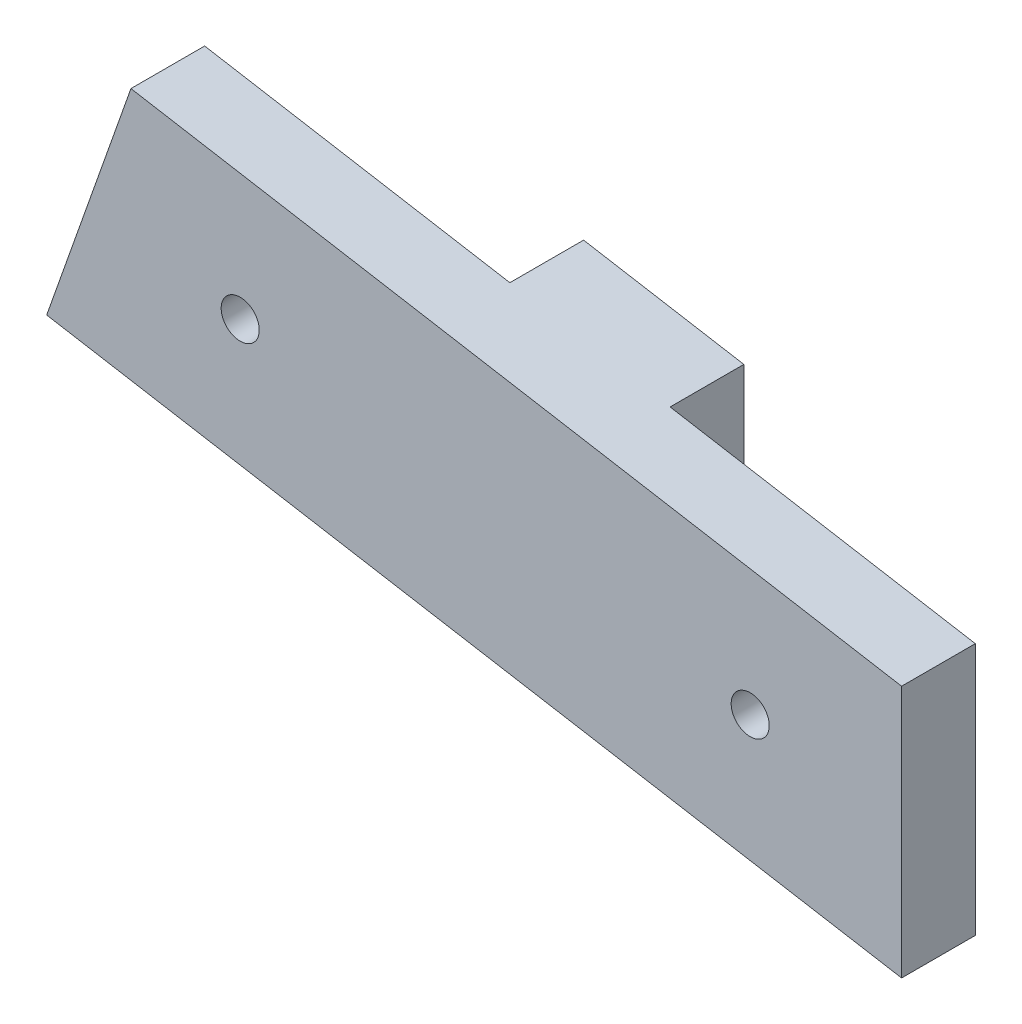
SolidWorks part; units mm, degrees
ref_plane "Спереди" through (0, 0, 0) normal (0, 0, 1) x (1, 0, 0)
ref_plane "Сверху" through (0, 0, 0) normal (0, 1, 0) x (1, 0, 0)
ref_plane "Справа" through (0, 0, 0) normal (1, 0, 0) x (0, 0, -1)
sketch "Эскиз1" plane through (0, 0, 0) normal (0, 0, 1) x (1, 0, 0)
  line L0 (-114.3235, 125.814) -> (-183.8951, 137.7528)
  line L1 (-183.8951, 137.7528) -> (-177.0391, 157.1408)
  line L2 (-177.0391, 157.1408) -> (-114.3235, 146.3785)
  line L3 (-114.3235, 146.3785) -> (-114.3235, 125.814)
extrude "Бобышка-Вытянуть1" add sketch "Эскиз1" along normal blind 6
sketch "Эскиз2" plane through (0, 0, 0) normal (0, 0, -1) x (-1, 0, 0)
  line L0 (139.1604, 150.6407) -> (139.1604, 130.0761)
  line L4 (114.3235, 146.3785) -> (177.0391, 157.1408) construction
  line L5 (183.8951, 137.7528) -> (114.3235, 125.814) construction
  line L7 (139.1604, 130.0761) -> (159.0582, 133.4907)
  line L8 (159.0582, 133.4907) -> (152.2021, 152.8787)
  line L9 (152.2021, 152.8787) -> (139.1604, 150.6407)
  dimension "D1" = 25.2
  dimension "D2" = 25.2
  dimension "D3" = 25.2
  dimension "D4" = 25.2
extrude "Бобышка-Вытянуть2" add sketch "Эскиз2" along normal blind 6
sketch "Эскиз3" plane through (0, 0, 0) normal (0, 0, -1) x (-1, 0, 0)
  circle A0 centre (126.6434, 138.2104) radius 1.55
  circle A1 centre (168.1472, 145.3327) radius 1.55
extrude "Вырез-Вытянуть1" cut sketch "Эскиз3" against normal through all
